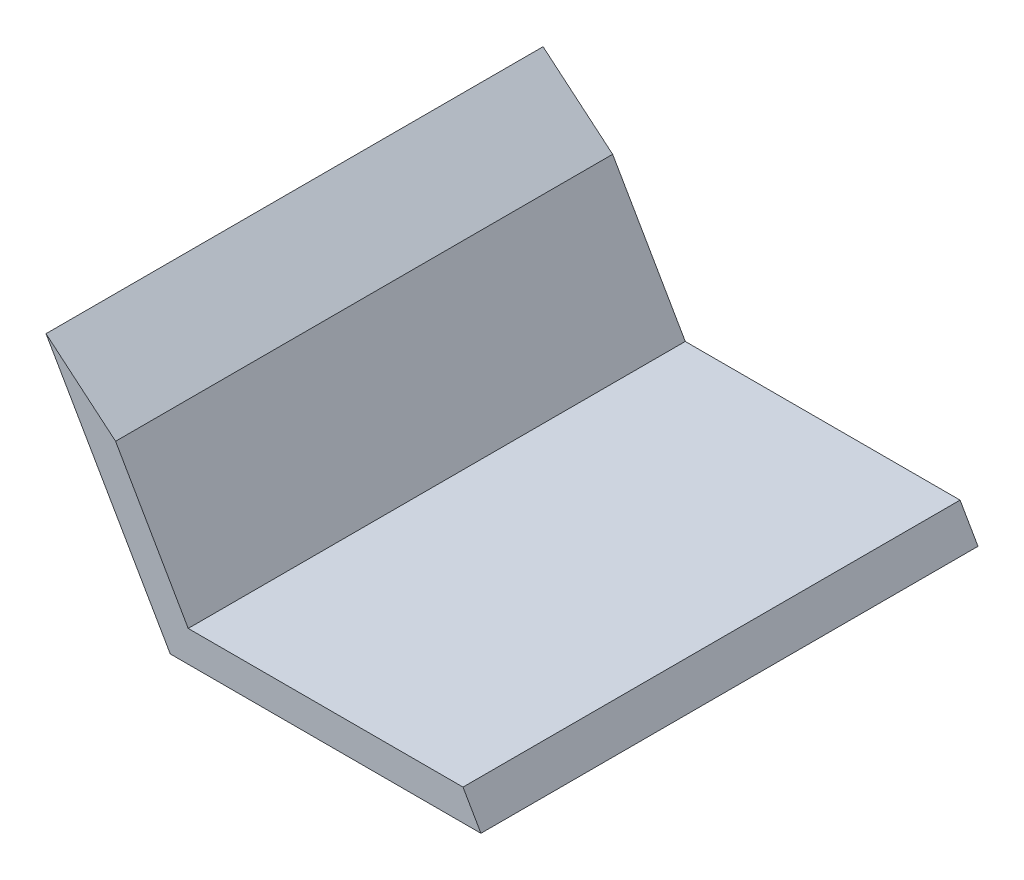
SolidWorks part; units mm, degrees
ref_plane "Front Plane" through (0, 0, 0) normal (0, 0, 1) x (1, 0, 0)
ref_plane "Top Plane" through (0, 0, 0) normal (0, 1, 0) x (1, 0, 0)
ref_plane "Right Plane" through (0, 0, 0) normal (1, 0, 0) x (0, 0, -1)
sketch "Sketch1" plane through (0, 0, 0) normal (0, 0, 1) x (1, 0, 0)
  line L0 (0, 0) -> (-6.35, 10.9985)
  line L1 (-6.35, 10.9985) -> (-4.5169, 10.9985)
  line L2 (-4.5169, 10.9985) -> (0.9165, 1.5875)
  line L3 (0.9165, 1.5875) -> (14.9585, 1.5875)
  line L5 (15.875, 0) -> (0, 0)
  line L6 (15.875, 0) -> (14.9585, 1.5875)
  point P5 (11.4562, 1.5231)
  dimension "D1" = 120
  dimension "D2" = 1.5875
  dimension "D3" = 12.7
  dimension "D4" = 15.875
  dimension "D5" = 60
  dimension "D6" = 1.5875
extrude "Boss-Extrude1" add sketch "Sketch1" along normal blind 25.4
sketch "Sketch2" plane through (0, 0, 25.4) normal (0, 0, 1) x (1, 0, 0)
  line L0 (-6.35, 10.9985) -> (-2.7944, 8.015)
  line L1 (0.9165, 1.5875) -> (-4.5169, 10.9985) construction
  line L2 (-2.7944, 8.015) -> (-4.5169, 10.9985)
  line L3 (-4.5169, 10.9985) -> (-6.35, 10.9985)
  dimension "D1" = 40
extrude "Cut-Extrude1" cut sketch "Sketch2" against normal through all
